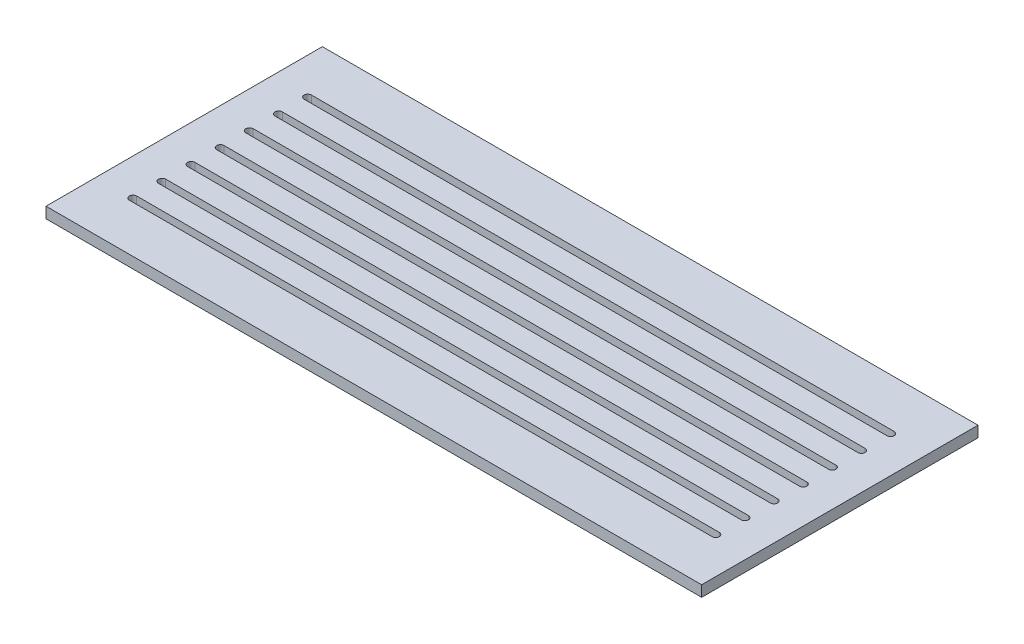
SolidWorks part; units mm, degrees
ref_plane "Front Plane" through (0, 0, 0) normal (0, 0, 1) x (1, 0, 0)
ref_plane "Top Plane" through (0, 0, 0) normal (0, 1, 0) x (1, 0, 0)
ref_plane "Right Plane" through (0, 0, 0) normal (1, 0, 0) x (0, 0, -1)
sketch "Sketch1" plane through (0, 0, 0) normal (0, 1, 0) x (1, 0, 0)
  line L0 (-85.567, 25.3965) -> (74.433, 25.3965)
  line L1 (-95.567, 46.3965) -> (84.433, 46.3965)
  line L2 (-95.567, 46.3965) -> (-95.567, -29.4735)
  line L3 (-95.567, -29.4735) -> (84.433, -29.4735)
  line L4 (84.433, 46.3965) -> (84.433, -29.4735)
  line L5 (-85.567, 33.3965) -> (74.433, 33.3965)
  line L6 (-85.567, 23.3965) -> (74.433, 23.3965)
  line L7 (-85.567, 31.3965) -> (74.433, 31.3965)
  line L8 (-85.567, 17.3965) -> (74.433, 17.3965)
  line L9 (-85.567, 15.3965) -> (74.433, 15.3965)
  line L10 (-85.567, 9.3965) -> (74.433, 9.3965)
  line L11 (-85.567, 7.3965) -> (74.433, 7.3965)
  line L12 (-85.567, 1.3965) -> (74.433, 1.3965)
  line L13 (-85.567, -0.6035) -> (74.433, -0.6035)
  line L14 (-85.567, -6.6035) -> (74.433, -6.6035)
  line L15 (-85.567, -8.6035) -> (74.433, -8.6035)
  line L16 (-85.567, -14.6035) -> (74.433, -14.6035)
  line L17 (-85.567, -16.6035) -> (74.433, -16.6035)
  line L90 (84.433, 8.4615) -> (104.4321, 8.4615) construction
  arc A0 (-85.567, 33.3965) -> (-85.567, 31.3965) centre (-85.567, 32.3965) ccw
  arc A1 (74.433, 33.3965) -> (74.433, 31.3965) centre (74.433, 32.3965) cw
  arc A2 (-85.567, 25.3965) -> (-85.567, 23.3965) centre (-85.567, 24.3965) ccw
  arc A3 (74.433, 25.3965) -> (74.433, 23.3965) centre (74.433, 24.3965) cw
  arc A4 (-85.567, 17.3965) -> (-85.567, 15.3965) centre (-85.567, 16.3965) ccw
  arc A5 (74.433, 17.3965) -> (74.433, 15.3965) centre (74.433, 16.3965) cw
  arc A6 (-85.567, 9.3965) -> (-85.567, 7.3965) centre (-85.567, 8.3965) ccw
  arc A7 (74.433, 9.3965) -> (74.433, 7.3965) centre (74.433, 8.3965) cw
  arc A8 (-85.567, 1.3965) -> (-85.567, -0.6035) centre (-85.567, 0.3965) ccw
  arc A9 (74.433, 1.3965) -> (74.433, -0.6035) centre (74.433, 0.3965) cw
  arc A10 (-85.567, -6.6035) -> (-85.567, -8.6035) centre (-85.567, -7.6035) ccw
  arc A11 (74.433, -6.6035) -> (74.433, -8.6035) centre (74.433, -7.6035) cw
  arc A12 (-85.567, -14.6035) -> (-85.567, -16.6035) centre (-85.567, -15.6035) ccw
  arc A13 (74.433, -14.6035) -> (74.433, -16.6035) centre (74.433, -15.6035) cw
  dimension "D1" = 180
  dimension "D2" = 75.87
  dimension "D3" = 160
  dimension "D4" = 2
  dimension "D5" = 7
  dimension "D6" = 13
extrude "Boss-Extrude1" add sketch "Sketch1" along normal blind 3
